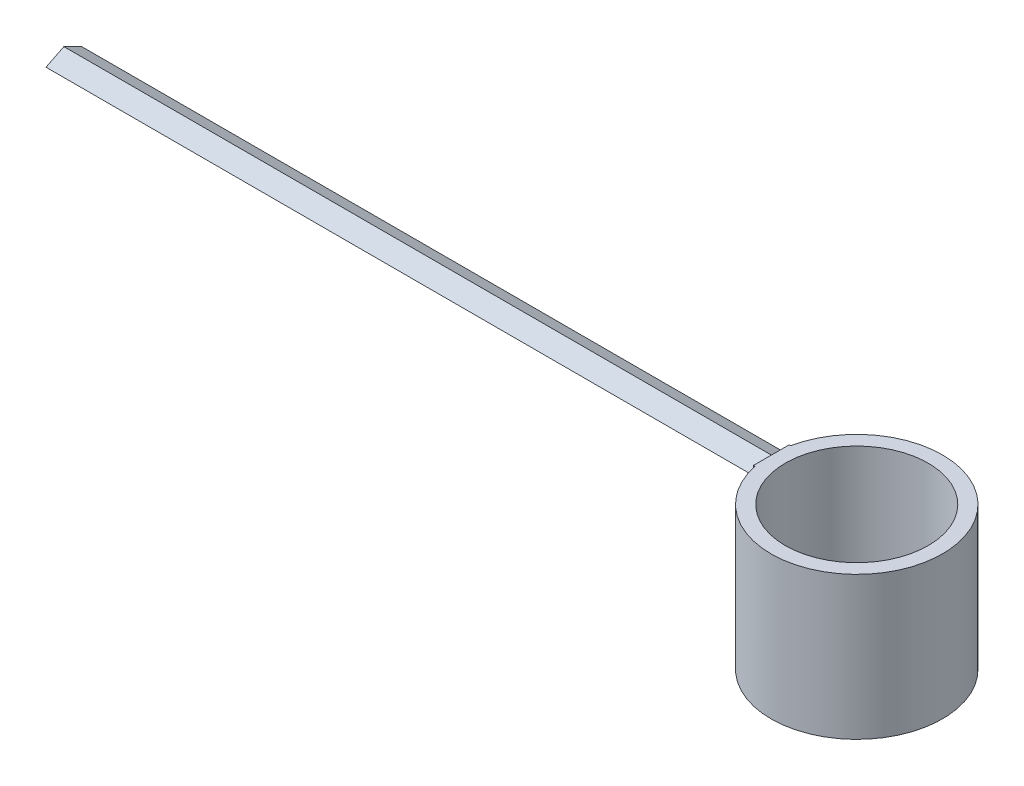
SolidWorks part; units mm, degrees
ref_plane "Front Plane" through (0, 0, 0) normal (0, 0, 1) x (1, 0, 0)
ref_plane "Top Plane" through (0, 0, 0) normal (0, 1, 0) x (1, 0, 0)
ref_plane "Right Plane" through (0, 0, 0) normal (1, 0, 0) x (0, 0, -1)
sketch "Sketch1" plane through (0, 0, 0) normal (0, 1, 0) x (1, 0, 0)
  circle A0 centre (0, 0) radius 1
  circle A1 centre (0, 0) radius 1.2
  dimension "D1" = 2
  dimension "D2" = 0.2
extrude "Boss-Extrude1" add sketch "Sketch1" along normal blind 2
sketch "Sketch2" plane through (0, 2, 0) normal (0, 1, 0) x (1, 0, 0)
  line L0 (-1.0947, -0.25) -> (-1.0947, 0.25)
  line L1 (-1.0947, 0.25) -> (-11.0947, 0.25)
  line L2 (-11.0947, 0.25) -> (-11.0947, -0.25)
  line L3 (-11.0947, -0.25) -> (-1.0947, -0.25)
  point P0 (-1.0947, 0)
  point P5 (0, 0)
  point P18 (0, 0)
  circle M13 centre (0, 0) radius 1.2
  dimension "D1" = 0.5
  dimension "D2" = 1.0947
  dimension "D3" = 10
  dimension "D4" = 0.5
extrude "Boss-Extrude3" add sketch "Sketch2" against normal blind 0.25 contours L2 L3 L1 M13
sketch "Sketch3" plane through (-11.0947, 0, 0) normal (-1, 0, 0) x (0, 0, 1)
  line L0 (-0.25, 1.875) -> (0, 2)
  line L1 (-0.25, 1.75) -> (-0.25, 2) construction
  line L2 (-0.25, 2) -> (0.25, 2) construction
  line L3 (0, 2) -> (0.25, 1.875)
  line L4 (0.25, 1.75) -> (0.25, 2) construction
  line L5 (0.25, 1.875) -> (0, 1.75)
  line L6 (-0.25, 1.75) -> (0.25, 1.75) construction
  line L7 (0, 1.75) -> (-0.25, 1.875)
extrude "Cut-Extrude3" cut sketch "Sketch3" against normal blind 9.9 flip side to cut
